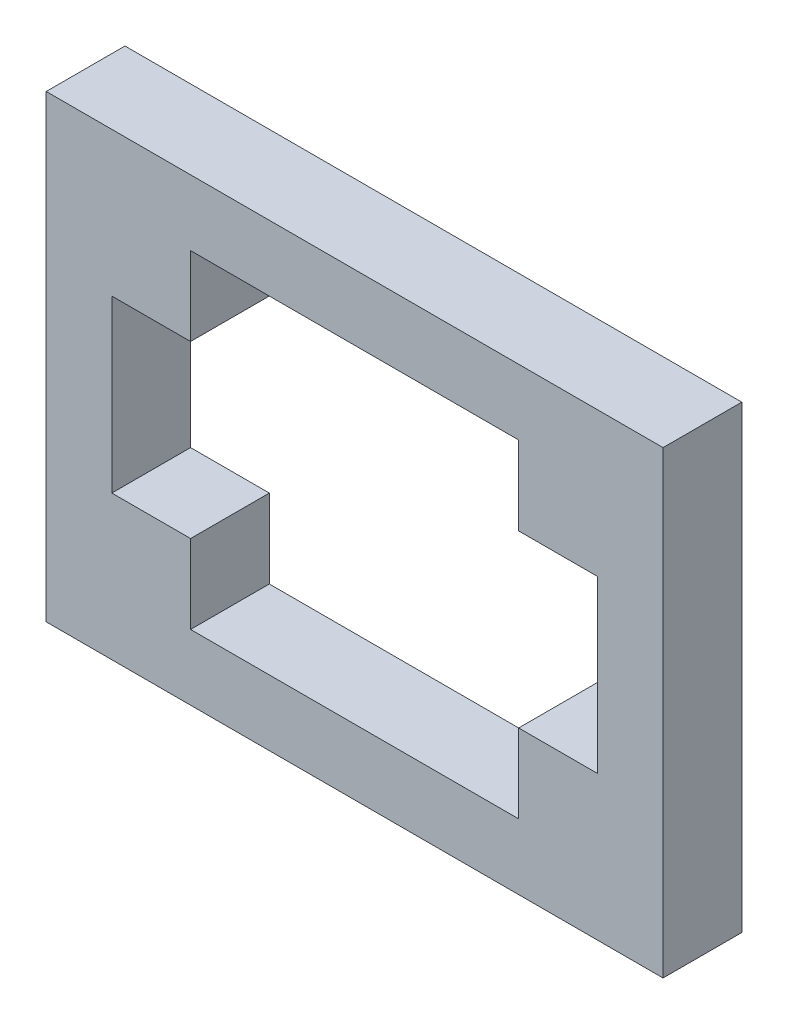
SolidWorks part; units mm, degrees
ref_plane "Plano frontal" through (0, 0, 0) normal (0, 0, 1) x (1, 0, 0)
ref_plane "Plano superior" through (0, 0, 0) normal (0, 1, 0) x (1, 0, 0)
ref_plane "Plano direito" through (0, 0, 0) normal (1, 0, 0) x (0, 0, -1)
sketch "Esboço1" plane through (0, 0, 0) normal (0, 0, 1) x (1, 0, 0)
  line L61 (0, 0) -> (47, 0)
  line L62 (0, 0) -> (0, 35)
  line L63 (0, 35) -> (47, 35)
  line L64 (47, 0) -> (47, 35)
  line L76 (11, 30) -> (36, 30)
  line L77 (5, 24) -> (5, 11)
  line L78 (11, 5) -> (36, 5)
  line L79 (42, 24) -> (42, 11)
  line L80 (5, 11) -> (11, 11)
  line L81 (11, 5) -> (11, 11)
  line L82 (42, 11) -> (36, 11)
  line L83 (36, 5) -> (36, 11)
  line L84 (42, 24) -> (36, 24)
  line L85 (36, 30) -> (36, 24)
  line L86 (5, 24) -> (11, 24)
  line L87 (11, 30) -> (11, 24)
  dimension "D1" = 35
  dimension "D2" = 47
  dimension "D3" = 5
  dimension "D4" = 5
  dimension "D5" = 6
  dimension "D6" = 6
  dimension "D7" = 6
  dimension "D8" = 6
  dimension "D9" = 13
  dimension "D10" = 25
extrude "Ressalto-extrusão1" add sketch "Esboço1" along normal blind 6
